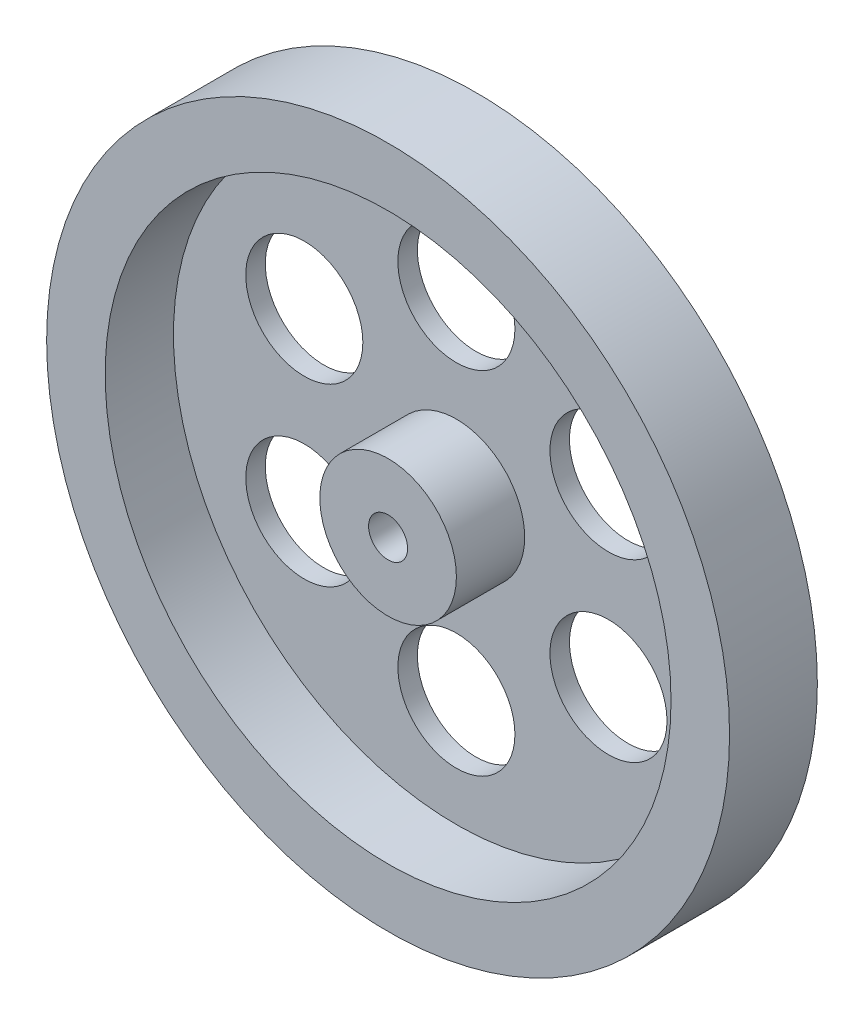
SolidWorks part; units mm, degrees
material "1060 Alloy"
ref_plane "Front Plane" through (0, 0, 0) normal (0, 0, 1) x (1, 0, 0)
ref_plane "Top Plane" through (0, 0, 0) normal (0, 1, 0) x (1, 0, 0)
ref_plane "Right Plane" through (0, 0, 0) normal (1, 0, 0) x (0, 0, -1)
sketch "Sketch1" plane through (0, 0, 0) normal (0, 0, 1) x (1, 0, 0)
  circle A0 centre (0, 0) radius 35
  dimension "D1" = 70
extrude "Boss-Extrude1" add sketch "Sketch1" along normal blind 9
sketch "Sketch2" plane through (0, 0, 9) normal (0, 0, 1) x (1, 0, 0)
  circle A1 centre (0, 0) radius 2
  dimension "D2" = 4
extrude "Cut-Extrude1" cut sketch "Sketch2" against normal through all and the other way through all
sketch "Sketch3" plane through (0, 0, 9) normal (0, 0, 1) x (1, 0, 0)
  circle A0 centre (0, 0) radius 7
  circle A1 centre (0, 0) radius 29
  circle A2 centre (0, 0) radius 35 construction
  dimension "D1" = 6
  dimension "D2" = 14
extrude "Cut-Extrude2" cut sketch "Sketch3" against normal blind 7
sketch "Sketch4" plane through (0, 0, 2) normal (0, 0, 1) x (1, 0, 0)
  circle A0 centre (0, 18) radius 6
  circle A1 centre (15.5885, 9) radius 6
  circle A2 centre (15.5885, -9) radius 6
  circle A3 centre (0, -18) radius 6
  circle A4 centre (-15.5885, -9) radius 6
  circle A5 centre (-15.5885, 9) radius 6
  point P15 (0, 0)
  dimension "D1" = 12
  dimension "D2" = 18
  dimension "D3" = 6
extrude "Cut-Extrude3" cut sketch "Sketch4" against normal through all
